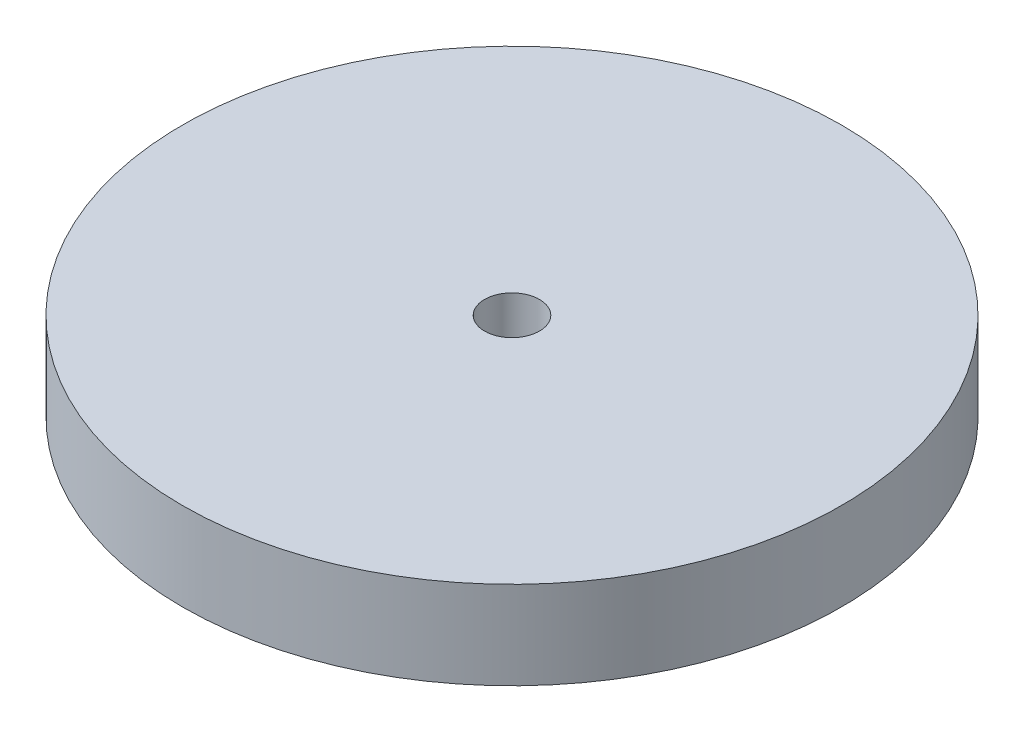
SolidWorks part; units mm, degrees
ref_plane "Front Plane" through (0, 0, 0) normal (0, 0, 1) x (1, 0, 0)
ref_plane "Top Plane" through (0, 0, 0) normal (0, 1, 0) x (1, 0, 0)
ref_plane "Right Plane" through (0, 0, 0) normal (1, 0, 0) x (0, 0, -1)
sketch "Sketch1" plane through (0, 0, 0) normal (0, 1, 0) x (1, 0, 0)
  circle A0 centre (0, 0) radius 30
  dimension "D1" = 60
extrude "Boss-Extrude1" add sketch "Sketch1" along normal blind 8
sketch "Sketch2" plane through (0, 8, 0) normal (0, 1, 0) x (1, 0, 0)
  circle A0 centre (0, 0) radius 2.5
  dimension "D1" = 5
extrude "Cut-Extrude1" cut sketch "Sketch2" against normal blind 10
